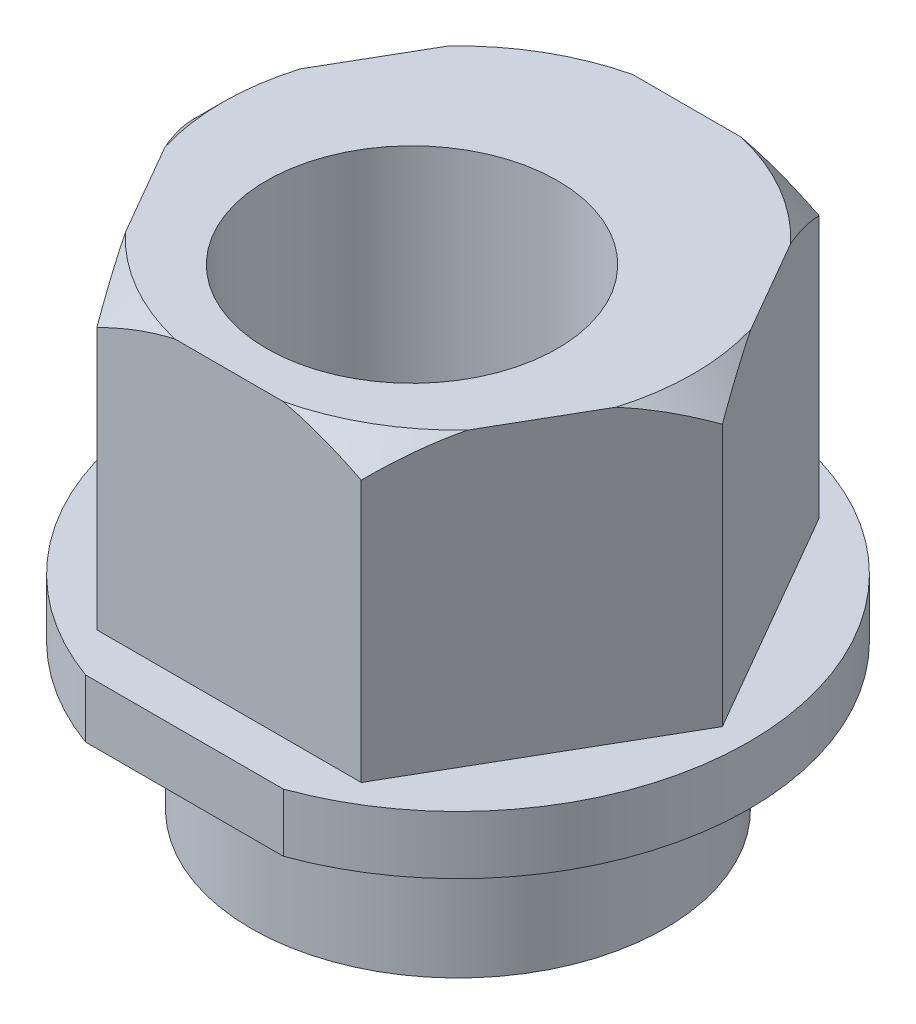
SolidWorks part; units mm, degrees
material "AISI 304"
ref_plane "Front Plane" through (0, 0, 0) normal (0, 0, 1) x (1, 0, 0)
ref_plane "Top Plane" through (0, 0, 0) normal (0, 1, 0) x (1, 0, 0)
ref_plane "Right Plane" through (0, 0, 0) normal (1, 0, 0) x (0, 0, -1)
sketch "Sketch1" plane through (0, 0, 0) normal (0, 1, 0) x (1, 0, 0)
  line L1 (4.5437, 0) -> (2.2719, 3.935)
  line L2 (2.2719, 3.935) -> (-2.2719, 3.935)
  line L3 (-2.2719, 3.935) -> (-4.5437, 0)
  line L4 (-4.5437, 0) -> (-2.2719, -3.935)
  line L5 (-2.2719, -3.935) -> (2.2719, -3.935)
  line L6 (2.2719, -3.935) -> (4.5437, 0)
  circle A0 centre (0, 0) radius 3.935 construction
  dimension "D1" = 7.87
extrude "Boss-Extrude1" add sketch "Sketch1" along normal blind 5
sketch "Sketch2" plane through (0, 0, 0) normal (0, 1, 0) x (1, 0, 0)
  circle A0 centre (0, 0) radius 5
  dimension "D1" = 10
extrude "Boss-Extrude2" add sketch "Sketch2" against normal blind 1
sketch "Sketch3" plane through (0, -1, 0) normal (0, -1, 0) x (1, 0, 0)
  circle A0 centre (0, 0) radius 3.555
  dimension "D1" = 7.11
extrude "Boss-Extrude3" add sketch "Sketch3" along normal blind 2.5
sketch "Sketch4" plane through (0, 5, 0) normal (0, 1, 0) x (1, 0, 0)
  line L0 (0, 0) -> (0, -0.79) construction
  circle A0 centre (0, -0.79) radius 2.5
  dimension "D1" = 5
  dimension "D2" = 0.79
extrude "Cut-Extrude1" cut sketch "Sketch4" against normal through all
sketch "Sketch5" plane through (0, 0, 0) normal (0, 1, 0) x (1, 0, 0)
  line L0 (-1.7, -4.7021) -> (1.7, -4.7021)
  circle A0 centre (0, 0) radius 5 construction
  arc A1 (-1.7, -4.7021) -> (1.7, -4.7021) centre (0, 0) ccw
  dimension "D1" = 3.4
extrude "Cut-Extrude2" cut sketch "Sketch5" against normal through all
sketch "Sketch6" plane through (0, 0, 0) normal (0, 0, 1) x (1, 0, 0)
  line L0 (0, 0) -> (0, 6.4706) construction
  line L1 (4.0437, 5) -> (4.5437, 5)
  line L2 (2.2719, 5) -> (4.5437, 5) construction
  line L3 (4.5437, 5) -> (4.5437, 4.5)
  line L4 (4.5437, 5) -> (4.5437, 0) construction
  line L5 (4.5437, 4.5) -> (4.0437, 5)
  dimension "D1" = 0.5
revolve "Cut-Revolve1" cut sketch "Sketch6" angle 360 about L0
